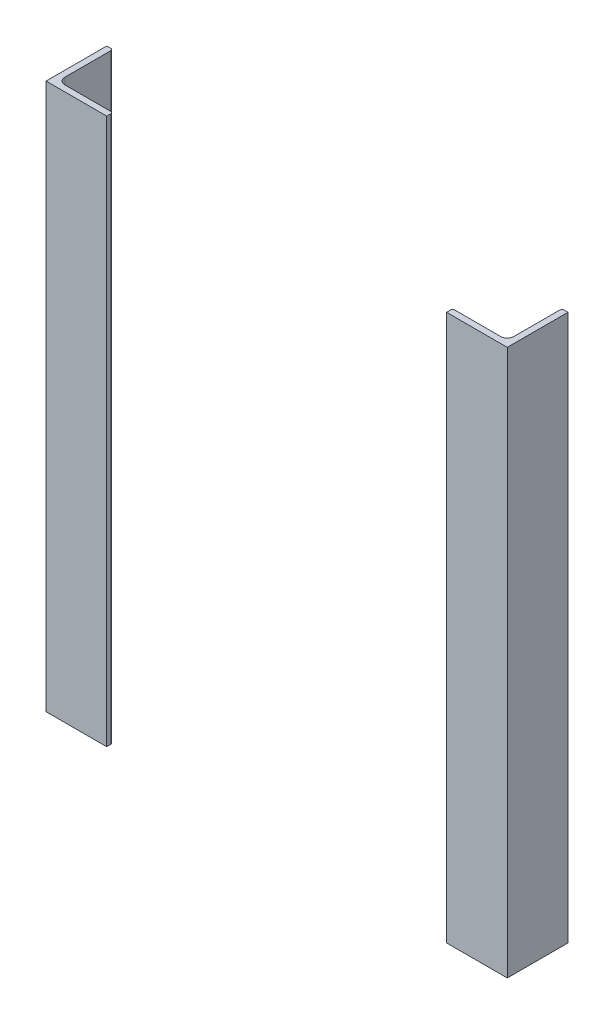
SolidWorks part; units mm, degrees
ref_plane "前视基准面" through (0, 0, 0) normal (0, 0, 1) x (1, 0, 0)
ref_plane "上视基准面" through (0, 0, 0) normal (0, 1, 0) x (1, 0, 0)
ref_plane "右视基准面" through (0, 0, 0) normal (1, 0, 0) x (0, 0, -1)
sketch "草图1" plane through (0, 0, 0) normal (0, 0, 1) x (1, 0, 0)
  line L0 (-190, 0) -> (-190, -450)
  line L1 (0, 0) -> (0, -285.6985) construction
  line L2 (190, 0) -> (190, -450)
  dimension "D1" = 380
  dimension "D2" = 450
  dimension "D3" = 0
other "L angle (equal) L ANGLE 5X5(1)"
ref_plane "基准面2" through (-190, 0, 0) normal (0, -1, 0) x (1, 0, 0)
sketch "Sketch1" plane through (-190, 0, 0) normal (0, -1, 0) x (1, 0, 0)
  line L0 (50, 0) -> (0, 0)
  line L1 (0, 0) -> (0, -50)
  line L2 (48.3333, -5) -> (10.5, -5)
  line L3 (5, -10.5) -> (5, -48.3333)
  line L4 (50, 0) -> (50, -3.3333)
  line L5 (0, -50) -> (3.3333, -50)
  arc A0 (50, -3.3333) -> (48.3333, -5) centre (48.3333, -3.3333) cw
  arc A1 (3.3333, -50) -> (5, -48.3333) centre (3.3333, -48.3333) ccw
  arc A2 (10.5, -5) -> (5, -10.5) centre (10.5, -10.5) ccw
  point P2 (25, 0)
  point P13 (0, -25)
  point P15 (0, 0)
  dimension "r1" = 1.6667
  dimension "r" = 5.5
  dimension "b" = 50
  dimension "d" = 5
